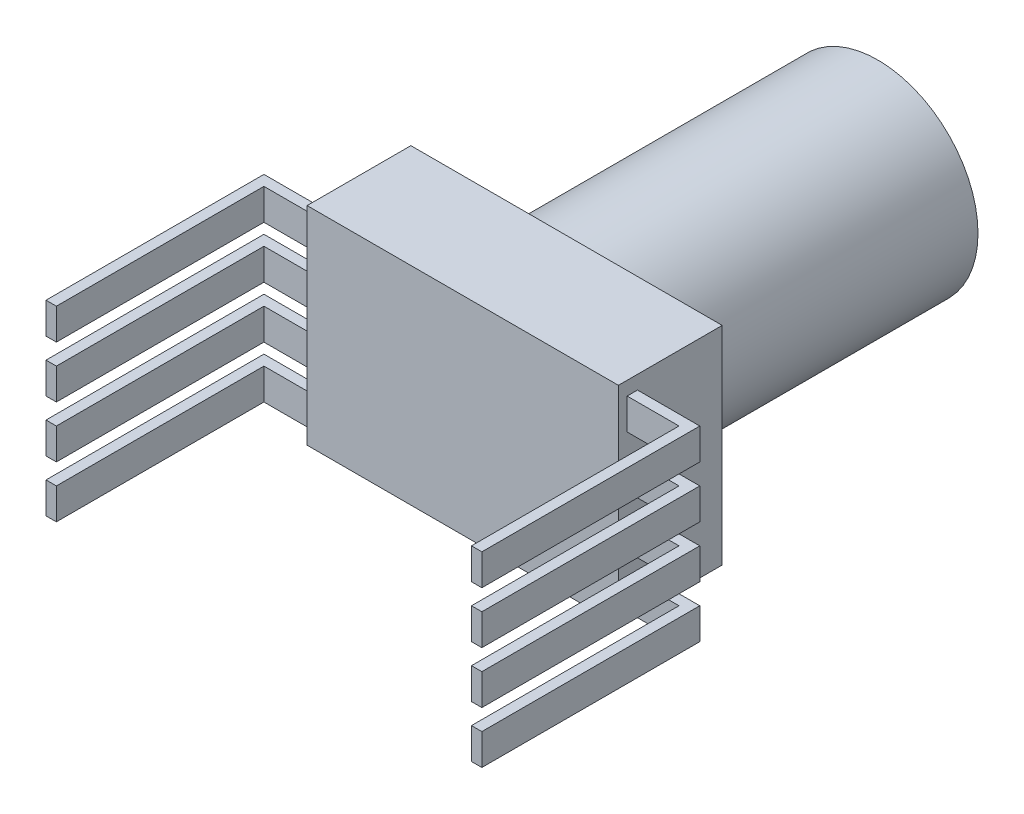
SolidWorks part; units mm, degrees
ref_plane "Front Plane" through (0, 0, 0) normal (0, 0, 1) x (1, 0, 0)
ref_plane "Top Plane" through (0, 0, 0) normal (0, 1, 0) x (1, 0, 0)
ref_plane "Right Plane" through (0, 0, 0) normal (1, 0, 0) x (0, 0, -1)
sketch "Sketch1" plane through (0, 0, 0) normal (0, 0, 1) x (1, 0, 0)
  circle A0 centre (0, 0) radius 4.825
  circle A1 centre (0, 0) radius 1.8182
extrude "Boss-Extrude1" add sketch "Sketch1" along normal blind 15
sketch "Sketch2" plane through (0, 0, 15) normal (0, 0, 1) x (1, 0, 0)
  line L1 (-7.5, -5) -> (7.5, -5)
  line L2 (-7.5, -5) -> (-7.5, 5)
  line L3 (-7.5, 5) -> (7.5, 5)
  line L4 (7.5, -5) -> (7.5, 5)
  line L5 (-7.5, -5) -> (7.5, 5) construction
  line L6 (-7.5, 5) -> (7.5, -5) construction
  point P0 (0, 0)
  dimension "D1" = 15
  dimension "D2" = 10
extrude "Boss-Extrude2" add sketch "Sketch2" along normal blind 5
sketch "Sketch3" plane through (-7.5, 0, 0) normal (-1, 0, 0) x (0, 0, 1)
  line L1 (19.5801, 4.3418) -> (19.0801, 4.3418)
  line L2 (19.5801, 4.3418) -> (19.5801, 2.8418)
  line L3 (19.5801, 2.8418) -> (19.0801, 2.8418)
  line L4 (19.0801, 4.3418) -> (19.0801, 2.8418)
  dimension "D1" = 0.5
  dimension "D2" = 1.5
extrude "Boss-Extrude3" add sketch "Sketch3" along normal blind 3
sketch "Sketch4" plane through (0, 0, 19.5801) normal (0, 0, 1) x (1, 0, 0)
  line L0 (-10.5, 4.3418) -> (-7.5, 4.3418) construction
  line L1 (-10.5, 2.8418) -> (-10, 2.8418)
  line L2 (-10.5, 2.8418) -> (-10.5, 4.3418)
  line L3 (-10.5, 4.3418) -> (-10, 4.3418)
  line L4 (-10, 2.8418) -> (-10, 4.3418)
  dimension "D1" = 0.5
extrude "Boss-Extrude4" add sketch "Sketch4" along normal blind 10
pattern_linear "LPattern2" count 4 spacing 2.5 along (0, -1, 0) of "Boss-Extrude3", "Boss-Extrude4"
mirror "Mirror1" about plane through (0, 0, 0) normal (1, 0, 0) of "LPattern2", "Boss-Extrude3", "Boss-Extrude4"
